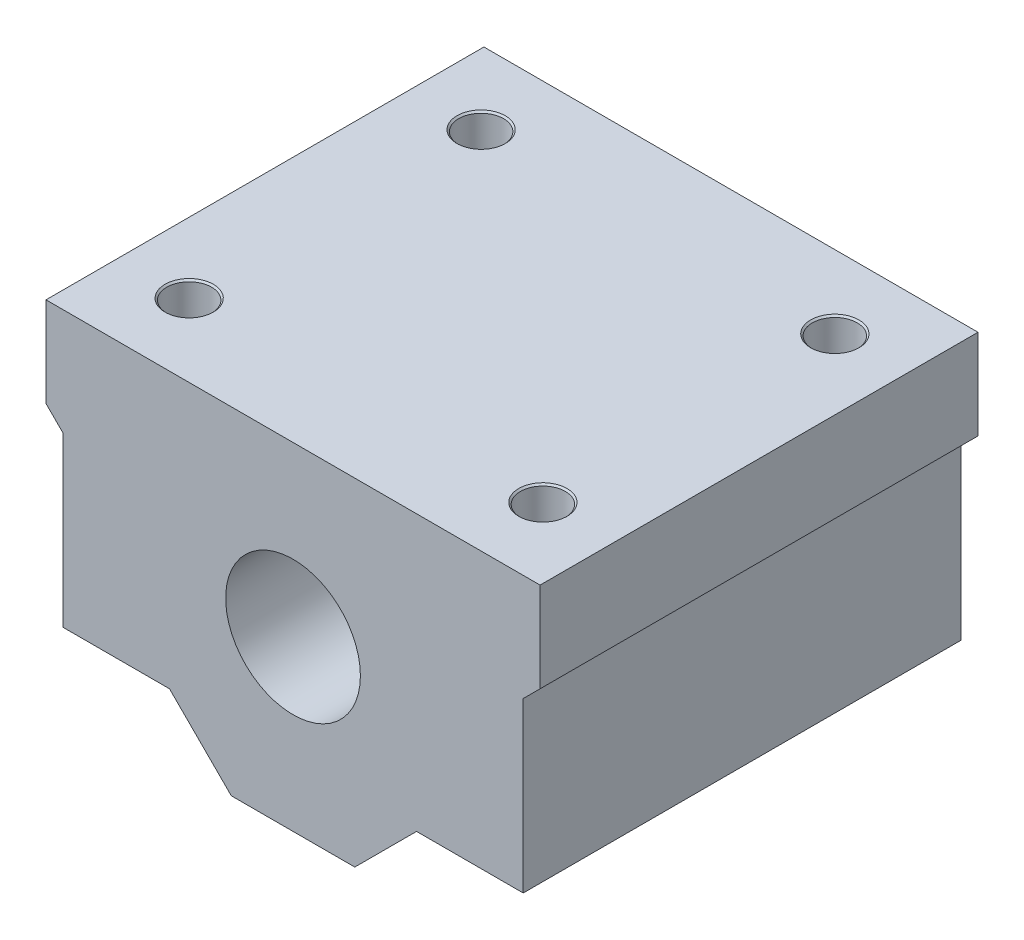
SolidWorks part; units mm, degrees
ref_plane "Ön Düzlem" through (0, 0, 0) normal (0, 0, 1) x (1, 0, 0)
ref_plane "Üst Düzlem" through (0, 0, 0) normal (0, 1, 0) x (1, 0, 0)
ref_plane "Sağ Düzlem" through (0, 0, 0) normal (1, 0, 0) x (0, 0, -1)
sketch "Çizim2" plane through (0, 0, 0) normal (0, 0, 1) x (1, 0, 0)
  line L0 (0, 19.2039) -> (0, -22.0439) construction
  line L1 (22, 15) -> (-22, 15)
  line L2 (-22, 15) -> (-22, 7)
  line L3 (-22, 7) -> (-20.5, 5.5)
  line L4 (-20.5, 5.5) -> (-20.5, -9.5)
  line L5 (-20.5, -9.5) -> (-11, -9.5)
  line L6 (-11, -9.5) -> (-5.5, -15)
  line L7 (-5.5, -15) -> (5.5, -15)
  line L8 (11, -9.5) -> (5.5, -15)
  line L9 (20.5, -9.5) -> (11, -9.5)
  line L10 (20.5, 5.5) -> (20.5, -9.5)
  line L11 (22, 7) -> (20.5, 5.5)
  line L12 (22, 15) -> (22, 7)
  circle A0 centre (0, 0) radius 6
  point P12 (-21.7392, -9.5)
  point P14 (-18.9823, 2.7886)
  point P15 (-19.9941, -9.5)
  point P16 (-13.6553, -9.5)
  point P17 (-22, 7)
  point P18 (-20, 3.868)
  point P19 (-9.1712, -15)
  point P20 (-7.0686, -15)
  point P21 (-20.5, 4.344)
  point P23 (0, -15)
  point P28 (0, 15)
  dimension "D1" = 12
  dimension "D2" = 15
  dimension "D3" = 22
  dimension "D4" = 30
  dimension "D5" = 24.5
  dimension "D6" = 8
  dimension "D7" = 1.5
  dimension "D8" = 9.5
  dimension "D9" = 135
  dimension "D10" = 135
extrude "Yükseklik-Ekstrüzyon1" add sketch "Çizim2" along normal blind 39
sketch "Çizim3" plane through (0, -9.5, 0) normal (0, -1, 0) x (1, 0, 0)
  line L0 (11, 6.7622) -> (20.5, 6.7622) construction
  line L1 (11, 39) -> (11, 0) construction
  line L2 (20.5, 39) -> (20.5, 0) construction
  line L3 (-20.5, 6.7622) -> (-11, 6.7622) construction
  line L4 (-20.5, 39) -> (-20.5, 0) construction
  line L5 (-11, 39) -> (-11, 0) construction
  line L6 (-20.5, 0) -> (-11, 0) construction
  circle A0 centre (-15.75, 6.5) radius 2
  circle A1 centre (-15.75, 32.5) radius 2
  circle A2 centre (15.75, 6.5) radius 2
  circle A3 centre (15.75, 32.5) radius 2
  point P20 (15.75, 6.7622)
  point P21 (-15.75, 6.7622)
  point P22 (0, 0)
  point P23 (0, 0)
  dimension "D3" = 4
  dimension "D1" = 26
  dimension "D2" = 6.5
extrude "Kes-Ekstrüzyon1" cut sketch "Çizim3" against normal blind 39
chamfer "Pah1" distance 0.15 angle 45 4 edges at (-15.75, 15, 4.5) (15.75, 15, 30.5) (15.75, 15, 4.5) (-15.75, 15, 30.5)
chamfer "Pah2" distance 1.5 angle 45 1 edges at (6, 0, 0)
